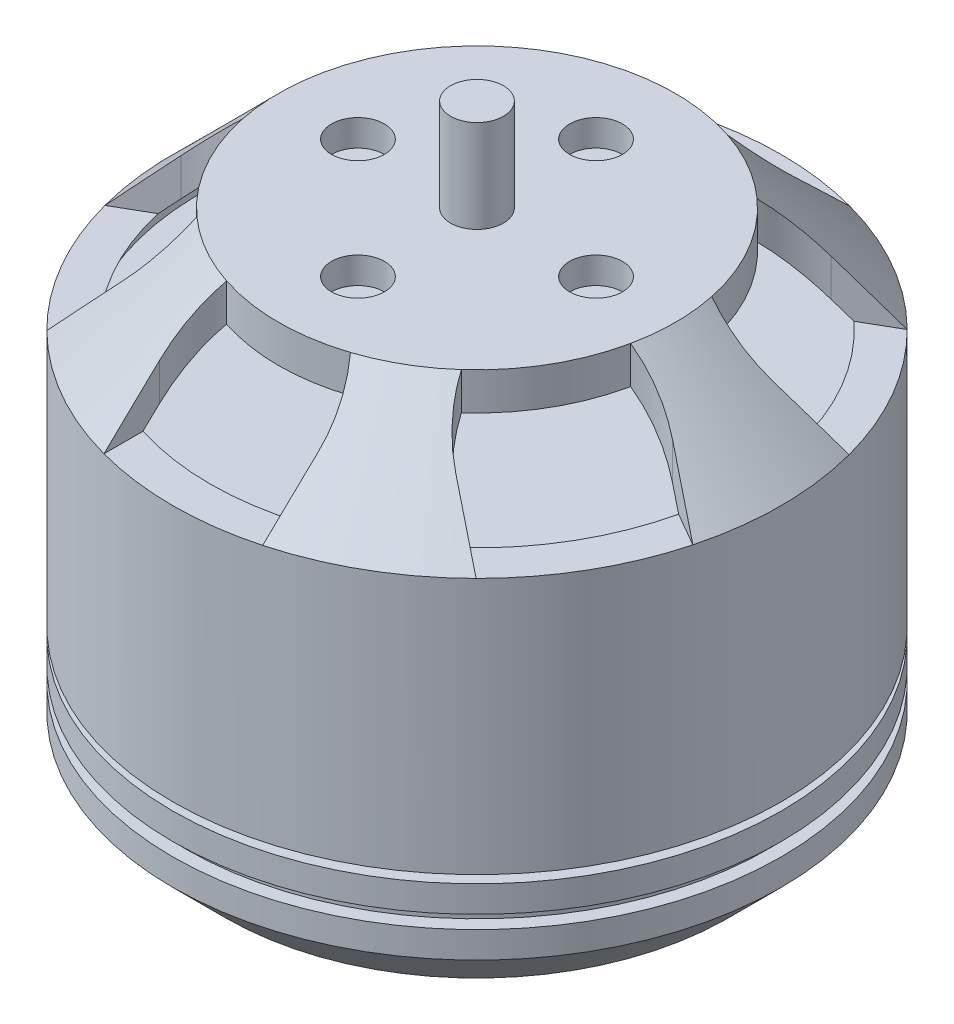
SolidWorks part; units mm, degrees
ref_plane "Front Plane" through (0, 0, 0) normal (0, 0, 1) x (1, 0, 0)
ref_plane "Top Plane" through (0, 0, 0) normal (0, 1, 0) x (1, 0, 0)
ref_plane "Right Plane" through (0, 0, 0) normal (1, 0, 0) x (0, 0, -1)
sketch "Sketch1" plane through (0, 0, 0) normal (0, 0, 1) x (1, 0, 0)
  line L0 (0, 20.294) -> (0, 0)
  line L1 (1, -1.706) -> (9.5, -1.706)
  line L2 (9.5, -1.706) -> (11.5, 0.294)
  line L3 (11.5, 0.294) -> (11.5, 1.294)
  line L4 (11.5, 12.794) -> (7.5, 16.794)
  line L5 (7.5, 16.794) -> (1, 16.794)
  line L6 (1, 16.794) -> (1, 20.294)
  line L7 (1, 20.294) -> (0, 20.294)
  line L8 (0, 0) -> (0, -3.506)
  line L9 (0, -3.506) -> (1, -3.506)
  line L10 (1, -3.506) -> (1, -1.706)
  line L11 (2, 15.794) -> (7.0858, 15.794)
  line L12 (7.0858, 15.794) -> (10.5, 12.3798)
  line L13 (10.5, 12.3798) -> (10.5, 11.9927)
  line L14 (10.5, 11.9927) -> (1, 11.9927)
  line L15 (1, 11.9927) -> (1, 14.794)
  line L16 (1, 14.794) -> (2, 14.794)
  line L17 (2, 14.794) -> (2, 15.794)
  line L18 (11.5, 1.294) -> (11, 1.294)
  line L19 (11, 1.294) -> (11, 1.794)
  line L20 (11, 1.794) -> (11.5, 1.794)
  line L21 (11.5, 2.794) -> (9.5, 2.794)
  line L22 (9.5, 2.794) -> (9.5, 3.094)
  line L23 (9.5, 3.094) -> (11.5, 3.094)
  line L24 (11.5, 3.094) -> (11.5, 12.794)
  line L25 (11.5, 1.794) -> (11.5, 2.794)
  point P25 (11.25, 1.794)
  dimension "D1" = 23.8
  dimension "D2" = 1.8
  dimension "D3" = 45
  dimension "D4" = 2
  dimension "D5" = 11.5
  dimension "D6" = 1
  dimension "D7" = 1
  dimension "D8" = 3.5
  dimension "D9" = 45
  dimension "D10" = 8.5
  dimension "D11" = 1
  dimension "D12" = 1
  dimension "D13" = 1
  dimension "D14" = 1
  dimension "D15" = 1
  dimension "D16" = 1
  dimension "D17" = 4
  dimension "D18" = 0.5
  dimension "D19" = 0.5
  dimension "D20" = 1
  dimension "D21" = 2
  dimension "D22" = 0.3
  dimension "D23" = 1
revolve "Revolve1" add sketch "Sketch1" angle 360 about L0
sketch "Sketch2" plane through (0, 16.794, 0) normal (0, 1, 0) x (1, 0, 0)
  line L0 (0, 0) -> (0, 9) construction
  line L1 (-3, 9) -> (-3, 16.1091)
  line L2 (-3, 16.1091) -> (3, 16.1091)
  line L3 (3, 16.1091) -> (3, 9)
  line L4 (6.2942, 7.0981) -> (12.4509, 10.6526)
  line L5 (12.4509, 10.6526) -> (15.4509, 5.4565)
  line L6 (15.4509, 5.4565) -> (9.2942, 1.9019)
  line L7 (9.2942, -1.9019) -> (15.4509, -5.4565)
  line L8 (15.4509, -5.4565) -> (12.4509, -10.6526)
  line L9 (12.4509, -10.6526) -> (6.2942, -7.0981)
  line L10 (3, -9) -> (3, -16.1091)
  line L11 (3, -16.1091) -> (-3, -16.1091)
  line L12 (-3, -16.1091) -> (-3, -9)
  line L13 (-6.2942, -7.0981) -> (-12.4509, -10.6526)
  line L14 (-12.4509, -10.6526) -> (-15.4509, -5.4565)
  line L15 (-15.4509, -5.4565) -> (-9.2942, -1.9019)
  line L16 (-9.2942, 1.9019) -> (-15.4509, 5.4565)
  line L17 (-15.4509, 5.4565) -> (-12.4509, 10.6526)
  line L18 (-12.4509, 10.6526) -> (-6.2942, 7.0981)
  circle A0 centre (0, 0) radius 4.5 construction
  circle A1 centre (0, 0) radius 9.559 construction
  circle A2 centre (0, -4.5) radius 1
  circle A3 centre (-4.5, 0) radius 1
  circle A4 centre (0, 4.5) radius 1
  circle A5 centre (4.5, 0) radius 1
  arc A6 (-2.999, 9.0764) -> (2.999, 9.0764) centre (0, 9) ccw
  arc A7 (6.3608, 7.1354) -> (9.3599, 1.9409) centre (7.7942, 4.5) ccw
  arc A8 (9.3599, -1.9409) -> (6.3608, -7.1354) centre (7.7942, -4.5) ccw
  arc A9 (2.999, -9.0764) -> (-2.999, -9.0764) centre (0, -9) ccw
  arc A10 (-6.3608, -7.1354) -> (-9.3599, -1.9409) centre (-7.7942, -4.5) ccw
  arc A11 (-9.3599, 1.9409) -> (-6.3608, 7.1354) centre (-7.7942, 4.5) ccw
  point P16 (0, 0)
  point P58 (0, 0)
  dimension "D1" = 9
  dimension "D3" = 2
  dimension "D5" = 6
  dimension "D2" = 9
  dimension "D4" = 4
  dimension "D6" = 6
extrude "Cut-Extrude1" cut sketch "Sketch2" against normal blind 4
sketch "Sketch3" plane through (0, -1.706, 0) normal (0, -1, 0) x (1, 0, 0)
  circle A0 centre (0, 0) radius 6 construction
  circle A1 centre (0, 0) radius 8 construction
  circle A2 centre (0, -6) radius 1
  circle A3 centre (0, 6) radius 1
  circle A4 centre (8, 0) radius 1
  circle A5 centre (-8, 0) radius 1
  dimension "D1" = 12
  dimension "D2" = 16
  dimension "D3" = 2
extrude "Cut-Extrude2" cut sketch "Sketch3" against normal blind 3
